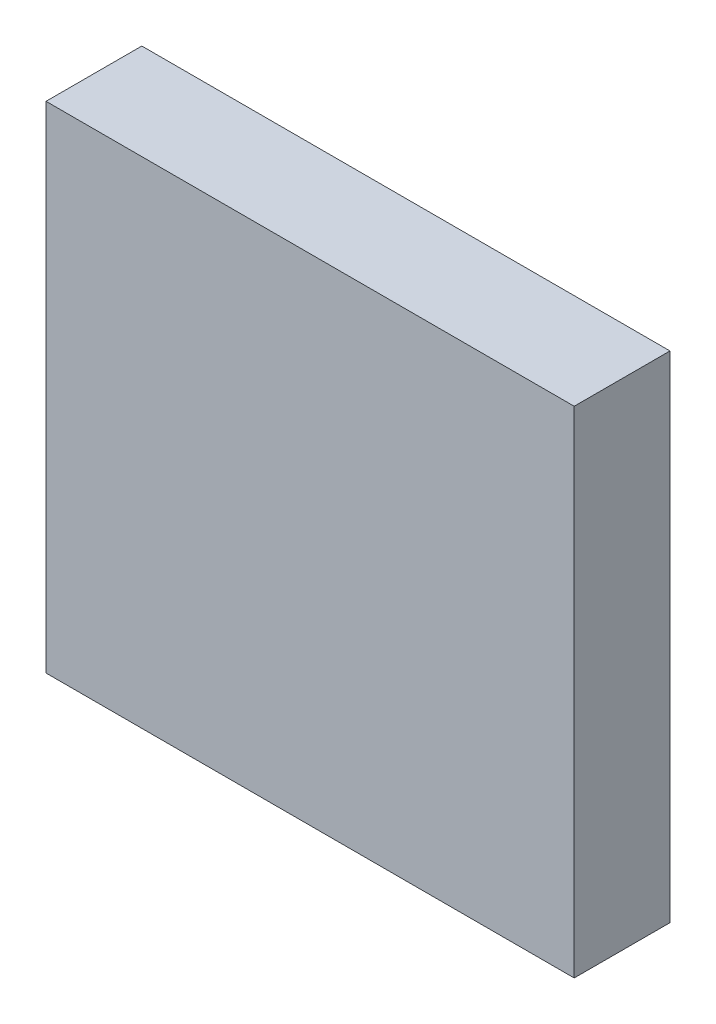
SolidWorks part; units mm, degrees
ref_plane "Front Plane" through (0, 0, 0) normal (1, 0, 0) x (0, 1, 0)
ref_plane "Top Plane" through (0, 0, 0) normal (0, 0, 1) x (0, 1, 0)
ref_plane "Right Plane" through (0, 0, 0) normal (0, 1, 0) x (-1, 0, 0)
sketch "Sketch1" plane through (0, 0, 0) normal (0, 0, 1) x (0, 1, 0)
  line L1 (0, 0) -> (90, 0)
  line L2 (0, 0) -> (0, 96)
  line L3 (0, 96) -> (90, 96)
  line L4 (90, 0) -> (90, 96)
  dimension "D1" = 90
  dimension "D2" = 96
extrude "Boss-Extrude1" add sketch "Sketch1" along normal blind 17.41
